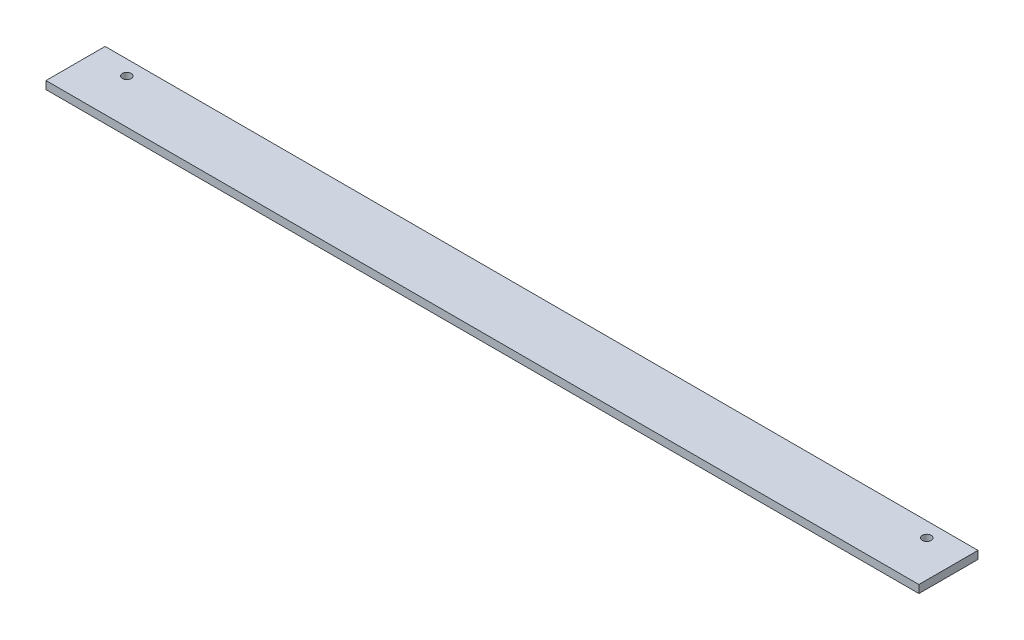
SolidWorks part; units mm, degrees
ref_plane "Спереди" through (0, 0, 0) normal (0, 0, 1) x (1, 0, 0)
ref_plane "Сверху" through (0, 0, 0) normal (0, 1, 0) x (1, 0, 0)
ref_plane "Справа" through (0, 0, 0) normal (1, 0, 0) x (0, 0, -1)
sketch "Эскиз1" plane through (0, 0, 0) normal (1, 0, 0) x (0, 0, -1)
  line L1 (-15, -2) -> (15, -2)
  line L2 (-15, -2) -> (-15, 2)
  line L3 (-15, 2) -> (15, 2)
  line L4 (15, -2) -> (15, 2)
  line L5 (-15, -2) -> (15, 2) construction
  line L6 (-15, 2) -> (15, -2) construction
  point P0 (0, 0)
  dimension "D1" = 4
  dimension "D2" = 30
extrude "Бобышка-Вытянуть1" add sketch "Эскиз1" along normal blind 443
sketch "Эскиз2" plane through (0, 2, 0) normal (0, 1, 0) x (1, 0, 0)
  line L0 (443, 15) -> (0, 15) construction
  line L1 (0, 15) -> (0, -15) construction
  line L2 (443, 15) -> (443, -15) construction
  circle A0 centre (18.5, 7.5) radius 2.25
  circle A1 centre (424.5, 7.5) radius 2.25
  dimension "D1" = 4.5
  dimension "D4" = 4.5
  dimension "D2" = 7.5
  dimension "D3" = 18.5
  dimension "D5" = 18.5
  dimension "D6" = 7.5
extrude "Вырез-Вытянуть1" cut sketch "Эскиз2" against normal through all
